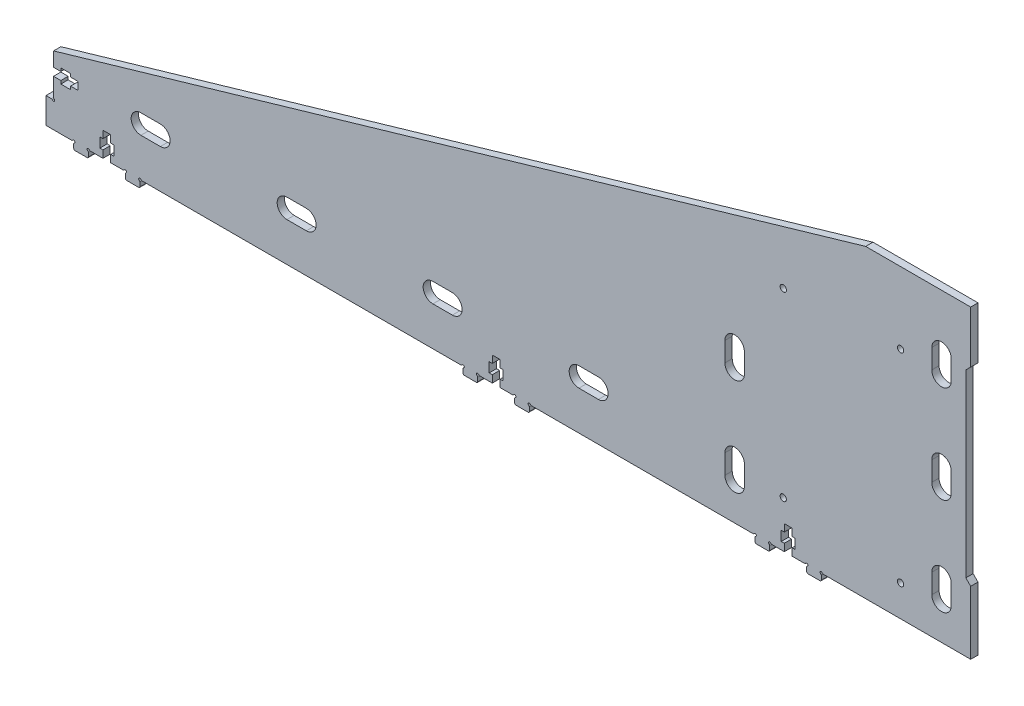
SolidWorks part; units mm, degrees
ref_plane "Alzado" through (0, 0, 0) normal (0, 0, 1) x (1, 0, 0)
ref_plane "Planta" through (0, 0, 0) normal (0, 1, 0) x (1, 0, 0)
ref_plane "Vista lateral" through (0, 0, 0) normal (1, 0, 0) x (0, 0, -1)
sketch "Model" plane through (0, 0, 0) normal (0, 0, 1) x (1, 0, 0)
  line L0 (115.0081, 287.9963) -> (107.0081, 287.9963)
  line L1 (107.0081, 279.9963) -> (115.0081, 279.9963)
  line L2 (175.0081, 287.9963) -> (167.0081, 287.9963)
  line L3 (167.0081, 279.9963) -> (175.0081, 279.9963)
  line L4 (235.0081, 287.9963) -> (227.0081, 287.9963)
  line L5 (227.0081, 279.9963) -> (235.0081, 279.9963)
  line L6 (295.0081, 287.9963) -> (287.0081, 287.9963)
  line L7 (287.0081, 279.9963) -> (295.0081, 279.9963)
  line L8 (355.0081, 278.9963) -> (355.0081, 286.9963)
  line L9 (347.0081, 286.9963) -> (347.0081, 278.9963)
  line L10 (355.0081, 318.9963) -> (355.0081, 326.9963)
  line L11 (347.0081, 326.9963) -> (347.0081, 318.9963)
  line L12 (440.0081, 318.9963) -> (440.0081, 326.9963)
  line L13 (432.0081, 326.9963) -> (432.0081, 318.9963)
  line L14 (440.0081, 358.9963) -> (440.0081, 366.9963)
  line L15 (432.0081, 366.9963) -> (432.0081, 358.9963)
  line L16 (387.4741, 263.9963) -> (448.0081, 263.9963)
  line L17 (448.0081, 263.9963) -> (448.0081, 289.9963)
  line L18 (448.0081, 289.9963) -> (446.0081, 291.9963)
  line L19 (446.0081, 291.9963) -> (446.0081, 365.9963)
  line L20 (446.0081, 365.9963) -> (448.0081, 367.9963)
  line L21 (448.0081, 367.9963) -> (448.0081, 389.3713)
  line L22 (448.0081, 389.3713) -> (404.8442, 389.3713)
  line L23 (404.8442, 389.3713) -> (403.1976, 388.8913)
  line L24 (403.1976, 388.8913) -> (81.1081, 294.9945)
  line L25 (81.1081, 294.9945) -> (71.1081, 292.0792)
  line L26 (71.1081, 292.0792) -> (71.1081, 286.2463)
  line L27 (71.1081, 286.2463) -> (74.1081, 286.2463)
  line L28 (74.1081, 286.2463) -> (74.1081, 287.5213)
  line L29 (74.1081, 287.5213) -> (78.1081, 287.5213)
  line L30 (78.1081, 287.5213) -> (78.1081, 286.2463)
  line L31 (78.1081, 286.2463) -> (81.1081, 286.2463)
  line L32 (81.1081, 286.2463) -> (81.1081, 283.0463)
  line L33 (81.1081, 283.0463) -> (78.1081, 283.0463)
  line L34 (78.1081, 283.0463) -> (78.1081, 281.7713)
  line L35 (78.1081, 281.7713) -> (74.1081, 281.7713)
  line L36 (74.1081, 281.7713) -> (74.1081, 283.0463)
  line L37 (74.1081, 283.0463) -> (71.1081, 283.0463)
  line L38 (71.1081, 283.0463) -> (71.1081, 275.5123)
  line L39 (70.2421, 274.6463) -> (68.0081, 274.6463)
  line L40 (68.0081, 274.6463) -> (68.0081, 263.9963)
  line L41 (68.0081, 263.9963) -> (78.5421, 263.9963)
  line L42 (79.4081, 263.1303) -> (79.4081, 261.4963)
  line L43 (79.9081, 260.9963) -> (84.9081, 260.9963)
  line L44 (85.4081, 261.4963) -> (85.4081, 263.1303)
  line L45 (86.2741, 263.9963) -> (91.4081, 263.9963)
  line L46 (91.4081, 263.9963) -> (91.4081, 266.9963)
  line L47 (91.4081, 266.9963) -> (90.1331, 266.9963)
  line L48 (90.1331, 266.9963) -> (90.1331, 270.9963)
  line L49 (90.1331, 270.9963) -> (91.4081, 270.9963)
  line L50 (91.4081, 270.9963) -> (91.4081, 273.9963)
  line L51 (91.4081, 273.9963) -> (94.6081, 273.9963)
  line L52 (94.6081, 273.9963) -> (94.6081, 270.9963)
  line L53 (94.6081, 270.9963) -> (95.8831, 270.9963)
  line L54 (95.8831, 270.9963) -> (95.8831, 266.9963)
  line L55 (95.8831, 266.9963) -> (94.6081, 266.9963)
  line L56 (94.6081, 266.9963) -> (94.6081, 263.9963)
  line L57 (94.6081, 263.9963) -> (99.7421, 263.9963)
  line L58 (100.6081, 263.1303) -> (100.6081, 261.4963)
  line L59 (101.1081, 260.9963) -> (106.1081, 260.9963)
  line L60 (106.6081, 261.4963) -> (106.6081, 263.1303)
  line L61 (107.4741, 263.9963) -> (238.5403, 263.9963)
  line L62 (238.5403, 263.9963) -> (238.5421, 263.9963)
  line L63 (239.4081, 263.1303) -> (239.4081, 261.4963)
  line L64 (239.9081, 260.9963) -> (244.9081, 260.9963)
  line L65 (245.4081, 261.4963) -> (245.4081, 263.1303)
  line L66 (246.2741, 263.9963) -> (251.4081, 263.9963)
  line L67 (251.4081, 263.9963) -> (251.4081, 266.9963)
  line L68 (251.4081, 266.9963) -> (250.1331, 266.9963)
  line L69 (250.1331, 266.9963) -> (250.1331, 270.9963)
  line L70 (250.1331, 270.9963) -> (251.4081, 270.9963)
  line L71 (251.4081, 270.9963) -> (251.4081, 273.9963)
  line L72 (251.4081, 273.9963) -> (254.6081, 273.9963)
  line L73 (254.6081, 273.9963) -> (254.6081, 270.9963)
  line L74 (254.6081, 270.9963) -> (255.8831, 270.9963)
  line L75 (255.8831, 270.9963) -> (255.8831, 266.9963)
  line L76 (255.8831, 266.9963) -> (254.6081, 266.9963)
  line L77 (254.6081, 266.9963) -> (254.6081, 263.9963)
  line L78 (254.6081, 263.9963) -> (259.7421, 263.9963)
  line L79 (260.6081, 263.1303) -> (260.6081, 261.4963)
  line L80 (261.1081, 260.9963) -> (266.1081, 260.9963)
  line L81 (266.6081, 261.4963) -> (266.6081, 263.1303)
  line L82 (267.4741, 263.9963) -> (358.5403, 263.9963)
  line L83 (358.5403, 263.9963) -> (358.5421, 263.9963)
  line L84 (359.4081, 263.1303) -> (359.4081, 261.4963)
  line L85 (359.9081, 260.9963) -> (364.9081, 260.9963)
  line L86 (365.4081, 261.4963) -> (365.4081, 263.1303)
  line L87 (366.2741, 263.9963) -> (371.4081, 263.9963)
  line L88 (371.4081, 263.9963) -> (371.4081, 266.9963)
  line L89 (371.4081, 266.9963) -> (370.1331, 266.9963)
  line L90 (370.1331, 266.9963) -> (370.1331, 270.9963)
  line L91 (370.1331, 270.9963) -> (371.4081, 270.9963)
  line L92 (371.4081, 270.9963) -> (371.4081, 273.9963)
  line L93 (371.4081, 273.9963) -> (374.6081, 273.9963)
  line L94 (374.6081, 273.9963) -> (374.6081, 270.9963)
  line L95 (374.6081, 270.9963) -> (375.8831, 270.9963)
  line L96 (375.8831, 270.9963) -> (375.8831, 266.9963)
  line L97 (375.8831, 266.9963) -> (374.6081, 266.9963)
  line L98 (374.6081, 266.9963) -> (374.6081, 263.9963)
  line L99 (374.6081, 263.9963) -> (379.7421, 263.9963)
  line L100 (380.6081, 263.1303) -> (380.6081, 261.4963)
  line L101 (381.1081, 260.9963) -> (386.1081, 260.9963)
  line L102 (386.6081, 261.4963) -> (386.6081, 263.1303)
  line L103 (440.0081, 278.9963) -> (440.0081, 286.9963)
  line L104 (432.0081, 286.9963) -> (432.0081, 278.9963)
  arc A0 (107.0081, 287.9963) -> (107.0081, 279.9963) centre (107.0081, 283.9963) ccw
  arc A1 (115.0081, 279.9963) -> (115.0081, 287.9963) centre (115.0081, 283.9963) ccw
  arc A2 (167.0081, 287.9963) -> (167.0081, 279.9963) centre (167.0081, 283.9963) ccw
  arc A3 (175.0081, 279.9963) -> (175.0081, 287.9963) centre (175.0081, 283.9963) ccw
  arc A4 (227.0081, 287.9963) -> (227.0081, 279.9963) centre (227.0081, 283.9963) ccw
  arc A5 (235.0081, 279.9963) -> (235.0081, 287.9963) centre (235.0081, 283.9963) ccw
  arc A6 (287.0081, 287.9963) -> (287.0081, 279.9963) centre (287.0081, 283.9963) ccw
  arc A7 (295.0081, 279.9963) -> (295.0081, 287.9963) centre (295.0081, 283.9963) ccw
  arc A8 (355.0081, 286.9963) -> (347.0081, 286.9963) centre (351.0081, 286.9963) ccw
  arc A9 (347.0081, 278.9963) -> (355.0081, 278.9963) centre (351.0081, 278.9963) ccw
  arc A10 (355.0081, 326.9963) -> (347.0081, 326.9963) centre (351.0081, 326.9963) ccw
  arc A11 (347.0081, 318.9963) -> (355.0081, 318.9963) centre (351.0081, 318.9963) ccw
  arc A12 (440.0081, 326.9963) -> (432.0081, 326.9963) centre (436.0081, 326.9963) ccw
  arc A13 (432.0081, 318.9963) -> (440.0081, 318.9963) centre (436.0081, 318.9963) ccw
  arc A14 (440.0081, 366.9963) -> (432.0081, 366.9963) centre (436.0081, 366.9963) ccw
  arc A15 (432.0081, 358.9963) -> (440.0081, 358.9963) centre (436.0081, 358.9963) ccw
  circle A16 centre (419.1695, 276.7848) radius 1.3
  circle A17 centre (419.1904, 359.9848) radius 1.3
  circle A18 centre (370.9755, 283.0078) radius 1.3
  circle A19 centre (370.9922, 357.5078) radius 1.3
  arc A20 (387.0411, 264.2463) -> (387.4741, 263.9963) centre (387.4741, 264.4963) ccw
  arc A21 (71.1081, 275.5123) -> (71.3581, 275.0793) centre (71.6081, 275.5123) ccw
  arc A22 (70.6751, 274.3963) -> (71.3581, 275.0793) centre (71.1081, 274.6463) ccw
  arc A23 (70.6751, 274.3963) -> (70.2421, 274.6463) centre (70.2421, 274.1463) ccw
  arc A24 (78.5421, 263.9963) -> (78.9751, 264.2463) centre (78.5421, 264.4963) ccw
  arc A25 (79.6581, 263.5633) -> (78.9751, 264.2463) centre (79.4081, 263.9963) ccw
  arc A26 (79.6581, 263.5633) -> (79.4081, 263.1303) centre (79.9081, 263.1303) ccw
  arc A27 (79.4081, 261.4963) -> (79.9081, 260.9963) centre (79.9081, 261.4963) ccw
  arc A28 (84.9081, 260.9963) -> (85.4081, 261.4963) centre (84.9081, 261.4963) ccw
  arc A29 (85.4081, 263.1303) -> (85.1581, 263.5633) centre (84.9081, 263.1303) ccw
  arc A30 (85.8411, 264.2463) -> (85.1581, 263.5633) centre (85.4081, 263.9963) ccw
  arc A31 (85.8411, 264.2463) -> (86.2741, 263.9963) centre (86.2741, 264.4963) ccw
  arc A32 (99.7421, 263.9963) -> (100.1751, 264.2463) centre (99.7421, 264.4963) ccw
  arc A33 (100.8581, 263.5633) -> (100.1751, 264.2463) centre (100.6081, 263.9963) ccw
  arc A34 (100.8581, 263.5633) -> (100.6081, 263.1303) centre (101.1081, 263.1303) ccw
  arc A35 (100.6081, 261.4963) -> (101.1081, 260.9963) centre (101.1081, 261.4963) ccw
  arc A36 (106.1081, 260.9963) -> (106.6081, 261.4963) centre (106.1081, 261.4963) ccw
  arc A37 (106.6081, 263.1303) -> (106.3581, 263.5633) centre (106.1081, 263.1303) ccw
  arc A38 (107.0411, 264.2463) -> (106.3581, 263.5633) centre (106.6081, 263.9963) ccw
  arc A39 (107.0411, 264.2463) -> (107.4741, 263.9963) centre (107.4741, 264.4963) ccw
  arc A40 (238.5421, 263.9963) -> (238.9751, 264.2463) centre (238.5421, 264.4963) ccw
  arc A41 (239.6581, 263.5633) -> (238.9751, 264.2463) centre (239.4081, 263.9963) ccw
  arc A42 (239.6581, 263.5633) -> (239.4081, 263.1303) centre (239.9081, 263.1303) ccw
  arc A43 (239.4081, 261.4963) -> (239.9081, 260.9963) centre (239.9081, 261.4963) ccw
  arc A44 (244.9081, 260.9963) -> (245.4081, 261.4963) centre (244.9081, 261.4963) ccw
  arc A45 (245.4081, 263.1303) -> (245.1581, 263.5633) centre (244.9081, 263.1303) ccw
  arc A46 (245.8411, 264.2463) -> (245.1581, 263.5633) centre (245.4081, 263.9963) ccw
  arc A47 (245.8411, 264.2463) -> (246.2741, 263.9963) centre (246.2741, 264.4963) ccw
  arc A48 (259.7421, 263.9963) -> (260.1751, 264.2463) centre (259.7421, 264.4963) ccw
  arc A49 (260.8581, 263.5633) -> (260.1751, 264.2463) centre (260.6081, 263.9963) ccw
  arc A50 (260.8581, 263.5633) -> (260.6081, 263.1303) centre (261.1081, 263.1303) ccw
  arc A51 (260.6081, 261.4963) -> (261.1081, 260.9963) centre (261.1081, 261.4963) ccw
  arc A52 (266.1081, 260.9963) -> (266.6081, 261.4963) centre (266.1081, 261.4963) ccw
  arc A53 (266.6081, 263.1303) -> (266.3581, 263.5633) centre (266.1081, 263.1303) ccw
  arc A54 (267.0411, 264.2463) -> (266.3581, 263.5633) centre (266.6081, 263.9963) ccw
  arc A55 (267.0411, 264.2463) -> (267.4741, 263.9963) centre (267.4741, 264.4963) ccw
  arc A56 (358.5421, 263.9963) -> (358.9751, 264.2463) centre (358.5421, 264.4963) ccw
  arc A57 (359.6581, 263.5633) -> (358.9751, 264.2463) centre (359.4081, 263.9963) ccw
  arc A58 (359.6581, 263.5633) -> (359.4081, 263.1303) centre (359.9081, 263.1303) ccw
  arc A59 (359.4081, 261.4963) -> (359.9081, 260.9963) centre (359.9081, 261.4963) ccw
  arc A60 (364.9081, 260.9963) -> (365.4081, 261.4963) centre (364.9081, 261.4963) ccw
  arc A61 (365.4081, 263.1303) -> (365.1581, 263.5633) centre (364.9081, 263.1303) ccw
  arc A62 (365.8411, 264.2463) -> (365.1581, 263.5633) centre (365.4081, 263.9963) ccw
  arc A63 (365.8411, 264.2463) -> (366.2741, 263.9963) centre (366.2741, 264.4963) ccw
  arc A64 (379.7421, 263.9963) -> (380.1751, 264.2463) centre (379.7421, 264.4963) ccw
  arc A65 (380.8581, 263.5633) -> (380.1751, 264.2463) centre (380.6081, 263.9963) ccw
  arc A66 (380.8581, 263.5633) -> (380.6081, 263.1303) centre (381.1081, 263.1303) ccw
  arc A67 (380.6081, 261.4963) -> (381.1081, 260.9963) centre (381.1081, 261.4963) ccw
  arc A68 (386.1081, 260.9963) -> (386.6081, 261.4963) centre (386.1081, 261.4963) ccw
  arc A69 (386.6081, 263.1303) -> (386.3581, 263.5633) centre (386.1081, 263.1303) ccw
  arc A70 (387.0411, 264.2463) -> (386.3581, 263.5633) centre (386.6081, 263.9963) ccw
  arc A71 (432.0081, 278.9963) -> (440.0081, 278.9963) centre (436.0081, 278.9963) ccw
  arc A72 (440.0081, 286.9963) -> (432.0081, 286.9963) centre (436.0081, 286.9963) ccw
extrude "Saliente-Extruir1" add sketch "Model" along normal blind 3
